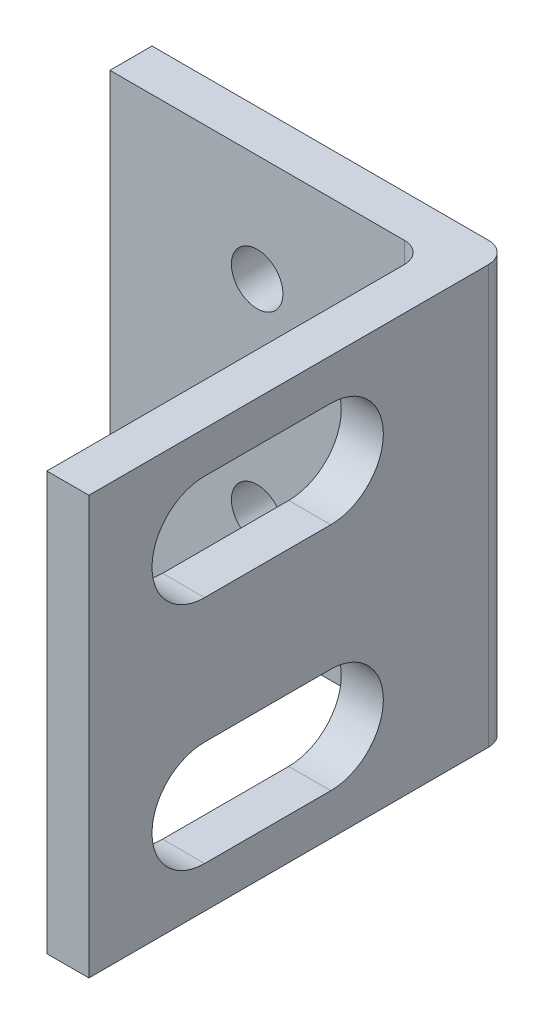
SolidWorks part; units mm, degrees
ref_plane "Front Plane" through (0, 0, 0) normal (0, 0, 1) x (1, 0, 0)
ref_plane "Top Plane" through (0, 0, 0) normal (0, 1, 0) x (1, 0, 0)
ref_plane "Right Plane" through (0, 0, 0) normal (1, 0, 0) x (0, 0, -1)
sketch "Sketch1" plane through (0, 0, 0) normal (0, 1, 0) x (1, 0, 0)
  line L1 (-2.113, 12.3401) -> (0.3116, 12.3401)
  line L2 (-0.6884, 9.3401) -> (-0.6884, -7.6599)
  line L3 (-0.6884, -7.6599) -> (1.3116, -7.6599)
  line L4 (1.3116, 11.3401) -> (1.3116, -7.6599)
  line L5 (-2.113, 12.3401) -> (1.3116, -7.6599) construction
  line L6 (-0.6884, -7.6599) -> (0.9499, 10.5703) construction
  line L7 (0.3116, 12.3401) -> (-15.6884, 12.3401)
  line L8 (1.3116, 11.3401) -> (1.3116, 10.9452)
  line L9 (-1.6884, 10.3401) -> (-15.6884, 10.3401)
  line L10 (-15.6884, 12.3401) -> (-15.6884, 10.3401)
  line L11 (0.6653, 12.2754) -> (-15.6884, 10.3401) construction
  line L12 (1.3116, 10.9452) -> (-15.6884, 12.3401) construction
  arc A0 (-0.6884, 9.3401) -> (-1.6884, 10.3401) centre (-1.6884, 9.3401) ccw
  arc A1 (1.3116, 11.3401) -> (0.3116, 12.3401) centre (0.3116, 11.3401) ccw
  arc A2 (1.3116, 11.3401) -> (0.3116, 12.3401) centre (0.3116, 11.3401) ccw
  point P0 (0, 0)
  point P9 (-5.7081, 11.5212)
  dimension "D4" = 1
  dimension "D5" = 1
  dimension "D6" = 1
  dimension "D1" = 17
  dimension "D2" = 2
  dimension "D3" = 2
  dimension "D7" = 20
extrude "Boss-Extrude1" add sketch "Sketch1" along normal blind 19.88 contours L7 L10 L9 L2 | L9 L4 L1 L2 | L4 L9 L2 L3
sketch "Sketch3" plane through (0, 0, -10.3401) normal (0, 0, 1) x (1, 0, 0)
  line L0 (-1.6884, 19.88) -> (-15.6884, 0) construction
  line L1 (-1.6884, 0) -> (-15.6884, 19.88) construction
  line L2 (-1.6884, 9.94) -> (-8.6884, 9.94) construction
  line L3 (-8.6884, 9.94) -> (-8.6884, 5.095) construction
  line L4 (-1.6884, 19.88) -> (-1.6884, 0) construction
  circle A0 centre (-8.6884, 5.095) radius 1.225
  circle A1 centre (-8.6884, 14.785) radius 1.225
  point P15 (0, 0)
  dimension "D3" = 2.45
  dimension "D1" = 4.845
extrude "Cut-Extrude1" cut sketch "Sketch3" against normal through all
sketch "Sketch4" plane through (-0.6884, 0, 0) normal (-1, 0, 0) x (0, 0, 1)
  line L0 (-9.3401, 19.88) -> (7.6599, 0) construction
  line L1 (7.6599, 19.88) -> (-9.3401, 0) construction
  line L2 (-0.8401, 9.94) -> (-0.8401, 15.4154) construction
  line L3 (-3.8401, 15.4154) -> (-0.8401, 15.4154) construction
  line L4 (-0.8401, 15.4154) -> (2.1599, 15.4154) construction
  line L5 (-3.8401, 17.9154) -> (2.1599, 17.9154)
  line L6 (-3.8401, 12.9154) -> (2.1599, 12.9154)
  line L7 (-0.8401, 9.94) -> (7.6599, 9.94) construction
  line L8 (7.6599, 19.88) -> (7.6599, 0) construction
  line L9 (-0.8401, 4.4646) -> (2.1599, 4.4646) construction
  line L10 (-3.8401, 4.4646) -> (-0.8401, 4.4646) construction
  line L11 (-3.8401, 6.9646) -> (2.1599, 6.9646)
  line L12 (-3.8401, 1.9646) -> (2.1599, 1.9646)
  circle A0 centre (2.1599, 15.4154) radius 2.5
  circle A1 centre (-3.8401, 15.4154) radius 2.5
  circle A2 centre (-3.8401, 4.4646) radius 2.5
  circle A3 centre (2.1599, 4.4646) radius 2.5
  point P2 (0, 9.94)
  point P3 (0, 0)
  point P6 (0, 0)
  point P7 (-0.0808, 9.94)
  point P31 (0, 0)
  point P32 (-0.8401, 9.94)
  point P37 (0, 0)
  dimension "D1" = 3
extrude "Cut-Extrude3" cut sketch "Sketch4" against normal through all contours A1 | A1 L6 A0 L5 | A0 | A2 | L12 A3 L11 A2 | A3 A2
